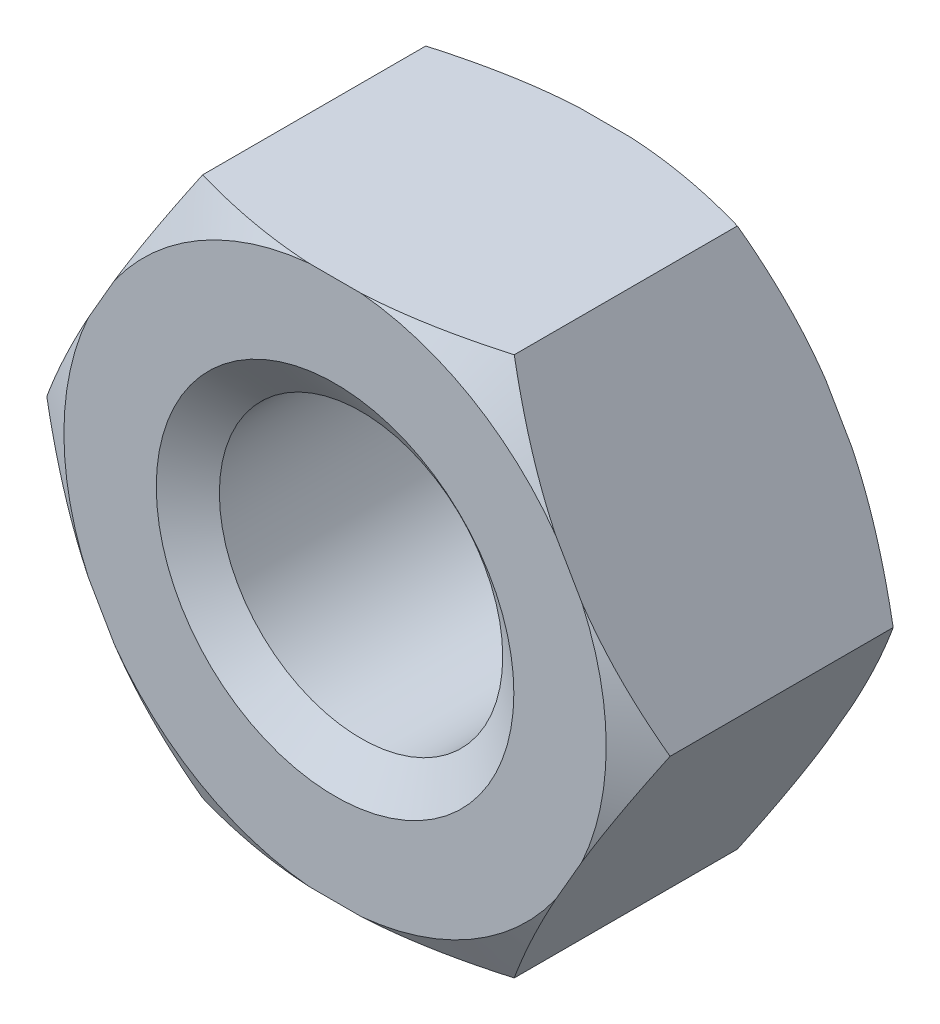
SolidWorks part; units mm, degrees
ref_plane "Спереди" through (0, 0, 0) normal (0, 0, 1) x (1, 0, 0)
ref_plane "Сверху" through (0, 0, 0) normal (0, 1, 0) x (1, 0, 0)
ref_plane "Справа" through (0, 0, 0) normal (1, 0, 0) x (0, 0, -1)
sketch "Эскиз1" plane through (0, 0, 0) normal (0, 0, 1) x (1, 0, 0)
  line L1 (4.6188, 0) -> (2.3094, 4)
  line L2 (2.3094, 4) -> (-2.3094, 4)
  line L3 (-2.3094, 4) -> (-4.6188, 0)
  line L4 (-4.6188, 0) -> (-2.3094, -4)
  line L5 (-2.3094, -4) -> (2.3094, -4)
  line L6 (2.3094, -4) -> (4.6188, 0)
  circle A0 centre (0, 0) radius 4 construction
  dimension "D1" = 8
extrude "Бобышка-Вытянуть1" add sketch "Эскиз1" along normal blind 4
sketch "Эскиз2" plane through (0, 0, 0) normal (0, 1, 0) x (1, 0, 0)
  line L0 (0, 0) -> (0, -4) construction
  line L1 (2.3094, -4) -> (-2.3094, -4) construction
  line L2 (-4.0188, 0) -> (-4.0188, 0.8128)
  line L5 (-4.0188, 0.8128) -> (-5.0166, 0.8128)
  line L7 (-4.0188, -4) -> (-4.6188, -3.6536)
  line L8 (-2.3094, -4) -> (-4.6188, -4) construction
  line L9 (-4.6188, -4) -> (-4.6188, 0) construction
  line L10 (-4.6188, -0.3464) -> (-4.0188, 0)
  line L11 (-2.3094, 0) -> (-4.6188, 0) construction
  line L12 (-5.0166, 0.8128) -> (-5.0166, -4.215)
  line L13 (-5.0166, -4.215) -> (-4.0188, -4.215)
  line L14 (-4.0188, -4.215) -> (-4.0188, -4)
  line L15 (-4.6188, -3.6536) -> (-4.6188, -0.3464)
  dimension "D1" = 30
  dimension "D2" = 0.6
revolve "Вырез-Повернуть2" cut sketch "Эскиз2" angle 360 about L0
hole_wizard "Отверстие обработанное метчиком M51" positions "Эскиз4" profile "Эскиз3" tap size "M5" standard "DIN" end condition through all
sketch "Эскиз4" plane through (0, 0, 0) normal (0, 0, -1) x (-1, 0, 0)
  point P0 (0, 0)
sketch "Эскиз3" plane through (0, 0, 0) normal (1, 0, 0) x (0, 1, 0)
  line L0 (0, 0) -> (0, 4)
  line L1 (0, 4) -> (2.65, 4)
  line L2 (2.1, 3.6149) -> (2.1, 0.3851)
  line L3 (2.1, 0.3851) -> (2.65, 0)
  line L5 (2.65, 0) -> (0, 0)
  line L6 (-2.1, 0.3851) -> (-2.65, 0) construction
  line L7 (2.65, 4) -> (2.1, 3.6149)
  line L8 (-2.65, 4) -> (-2.1, 3.6149) construction
  line L11 (0, -6.35) -> (0, 107.95) construction
  dimension "Диаметр проходного сверла" = 4.2
  dimension "Глубина проходного сверла" = 4
  dimension "Диаметр передней зенковки" = 5.3
  dimension "Угол передней зенковки" = 110
  dimension "Диаметр задней зенковки" = 5.3
  dimension "Угол задней зенковки" = 110
cosmetic thread "Отверстие резьбы1" parameters "D2"=5
